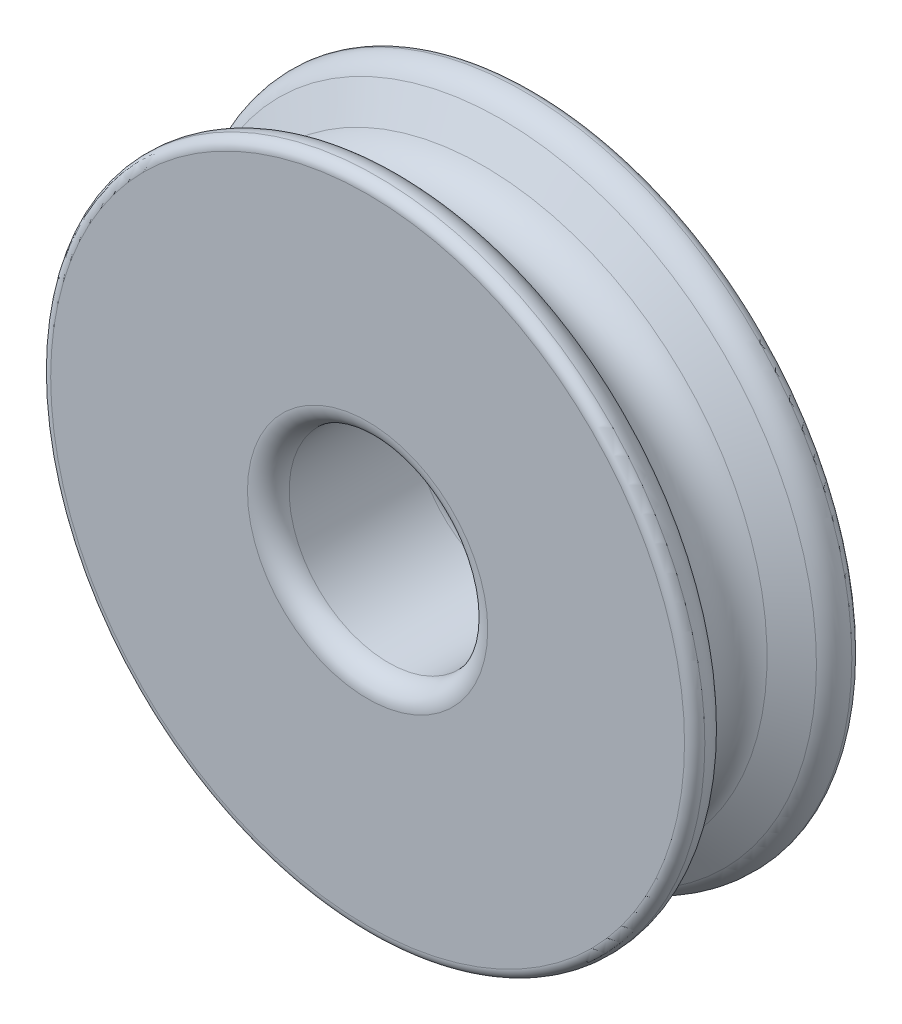
SolidWorks part; units mm, degrees
ref_plane "Front Plane" through (0, 0, 0) normal (0, 0, 1) x (1, 0, 0)
ref_plane "Top Plane" through (0, 0, 0) normal (0, 1, 0) x (1, 0, 0)
ref_plane "Right Plane" through (0, 0, 0) normal (1, 0, 0) x (0, 0, -1)
sketch "Sketch1" plane through (0, 0, 0) normal (1, 0, 0) x (0, 0, -1)
  line L0 (0, 0) -> (0, 17451.5356) construction
  line L1 (4, 0) -> (-4, 0)
  line L2 (-4, 0) -> (-4, 15.2006)
  line L3 (4, 0) -> (4, 15.2006)
  line L6 (-2.4257, 15.1015) -> (-1.5588, 13.6)
  line L7 (2.4257, 15.1015) -> (1.5588, 13.6)
  arc A0 (-4, 15.2006) -> (-3.525, 15.7) centre (-3.5, 15.2006) cw
  arc A1 (4, 15.2006) -> (3.525, 15.7) centre (3.5, 15.2006) ccw
  arc A2 (-3.525, 15.7) -> (-2.4257, 15.1015) centre (-3.465, 14.5015) cw
  arc A3 (3.525, 15.7) -> (2.4257, 15.1015) centre (3.465, 14.5015) ccw
  arc A4 (-1.5588, 13.6) -> (1.5588, 13.6) centre (0, 14.5) ccw
  point P6 (0, 0)
  point P18 (0, 12.7)
  dimension "D2" = 0.5
  dimension "D4" = 1.2
  dimension "D5" = 1.8
  dimension "D1" = 8
  dimension "D3" = 12.7
  dimension "D6" = 3
  dimension "D7" = 60
revolve "Revolve1" add sketch "Sketch1" angle 360 about L1
sketch "Sketch2" plane through (0, 0, 4) normal (0, 0, 1) x (1, 0, 0)
  circle A0 centre (0, 0) radius 4.7625
  circle A1 centre (0, 0) radius 15.2006
  circle A2 centre (0, 0) radius 15.2006
  dimension "D2" = 9.525
  dimension "D1" = 0
extrude "Cut-Extrude2" cut sketch "Sketch2" against normal through all contours A0
fillet "Fillet3" radius 1 2 edges at (4.7625, 0, -4) (4.7625, 0, 4)
